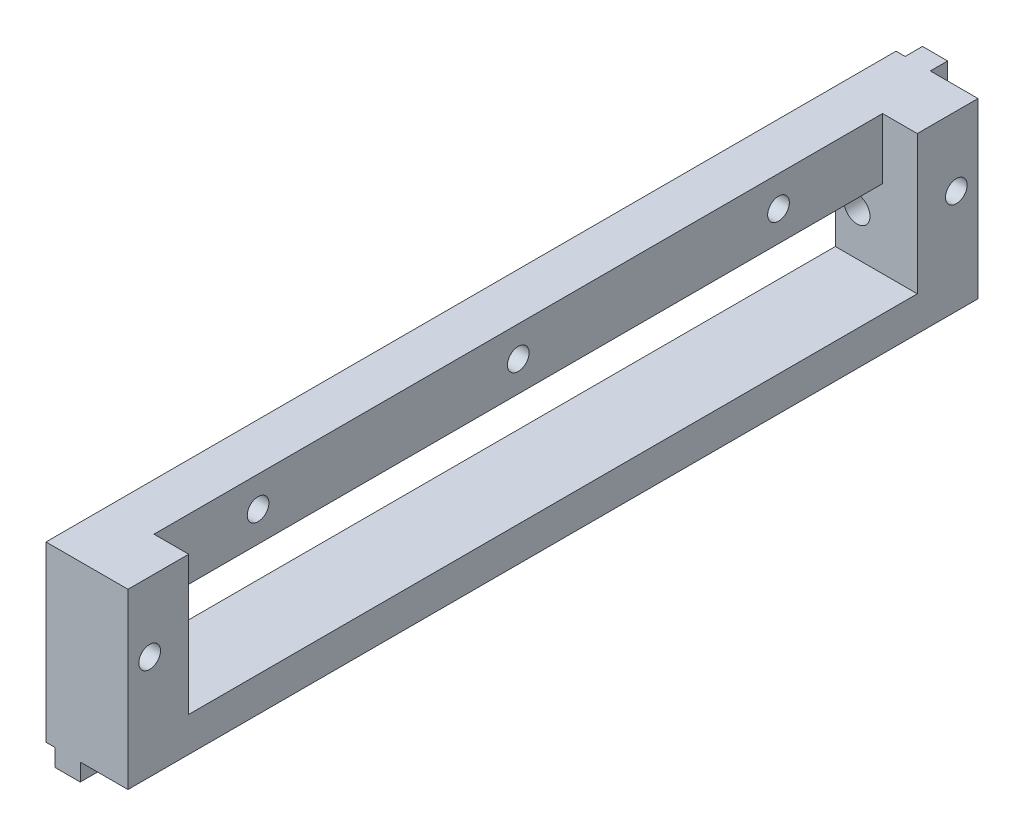
SolidWorks part; units mm, degrees
ref_plane "Front Plane" through (0, 0, 0) normal (0, 0, 1) x (1, 0, 0)
ref_plane "Top Plane" through (0, 0, 0) normal (0, 1, 0) x (1, 0, 0)
ref_plane "Right Plane" through (0, 0, 0) normal (1, 0, 0) x (0, 0, -1)
sketch "Esquisse1" plane through (0, 0, 0) normal (0, 0, 1) x (1, 0, 0)
  line L0 (0, 20) -> (9.45, 20)
  line L1 (9.45, 20) -> (9.45, 0)
  line L2 (9.45, 0) -> (3.95, 0)
  line L3 (3.95, 0) -> (3.95, -2)
  line L4 (3.95, -2) -> (1.05, -2)
  line L5 (1.05, -2) -> (1.05, 0)
  line L6 (1.05, 0) -> (0, 0)
  line L7 (0, 0) -> (0, 20)
  dimension "D1" = 5.5
  dimension "D2" = 20
  dimension "D3" = 2
  dimension "D4" = 2.9
  dimension "D5" = 1.05
  dimension "D6" = 9.45
extrude "Main" add sketch "Esquisse1" along normal mid plane 98
sketch "Esquisse2" plane through (9.45, 0, 0) normal (1, 0, 0) x (0, 0, -1)
  line L0 (-49, 0) -> (49, 0) construction
  line L1 (-46.5, 12) -> (46.5, 12) construction
  line L3 (-49, 20) -> (49, 20) construction
  circle A0 centre (46.5, 12) radius 1.25
  circle A1 centre (-46.5, 12) radius 1.25
  point P8 (0, 20)
  point P9 (0, 12)
  dimension "D1" = 93
  dimension "D3" = 2.5
  dimension "D2" = 12
extrude "HolesForLCDTop" cut sketch "Esquisse2" against normal through all
sketch "Sketch1" plane through (9.45, 0, 0) normal (1, 0, 0) x (0, 0, -1)
  line L0 (-49, 20) -> (49, 20) construction
  line L1 (42, 4) -> (-42, 4)
  line L2 (42, 4) -> (42, 20)
  line L3 (42, 20) -> (-42, 20)
  line L4 (-42, 4) -> (-42, 20)
  line L5 (49, 0) -> (49, 20) construction
  line L6 (-49, 0) -> (-49, 20) construction
  line L8 (-49, 0) -> (49, 0) construction
  point P8 (49, 10)
  point P11 (39, 3.337)
  dimension "D1" = 7
  dimension "D2" = 7
  dimension "D3" = 4
extrude "PowerBoardPinHoles" cut sketch "Sketch1" against normal blind 4
sketch "Sketch2" plane through (0, 0, 0) normal (-1, 0, 0) x (0, 0, 1)
  line L0 (49, 20) -> (-49, 20) construction
  circle A0 centre (0, 16.5) radius 1.25
  circle A1 centre (-30, 16.5) radius 1.25
  circle A2 centre (30, 16.5) radius 1.25
  point P3 (0, 20)
  dimension "D1" = 2.5
  dimension "D2" = 3.5
  dimension "D3" = 30
  dimension "D4" = 30
extrude "WindowFixHoles" cut sketch "Sketch2" against normal through all
sketch "Sketch3" plane through (0, 0, -49) normal (0, 0, -1) x (-1, 0, 0)
  line L0 (-9.45, 20) -> (0, 20) construction
  line L1 (-1.05, 0) -> (-3.95, 0)
  line L2 (-1.05, 0) -> (-1.05, 20)
  line L3 (-1.05, 20) -> (-3.95, 20)
  line L4 (-3.95, 0) -> (-3.95, 20)
  point P7 (-3.95, 0)
extrude "MakerBeamFix" add sketch "Sketch3" along normal blind 2
sketch "Sketch4" plane through (0, 0, -51) normal (0, 0, -1) x (-1, 0, 0)
  line L0 (-3.95, 0) -> (-1.05, 0) construction
  circle A0 centre (-2.5, 9) radius 1.5
  point P2 (-2.5, 0)
  point P3 (0, 0)
  dimension "D1" = 3
  dimension "D2" = 9
extrude "FixHoleForMakerBeam" cut sketch "Sketch4" against normal blind 20
sketch "Sketch5" plane through (5.45, 0, 0) normal (1, 0, 0) x (0, 0, -1)
  line L0 (42, 4) -> (42, 20) construction
  line L1 (-42, 4) -> (42, 4)
  line L2 (-42, 4) -> (-42, 13)
  line L3 (-42, 13) -> (42, 13)
  line L4 (42, 4) -> (42, 13)
  dimension "D1" = 9
extrude "HolesToHaveAccessToFixHole" cut sketch "Sketch5" against normal through all
